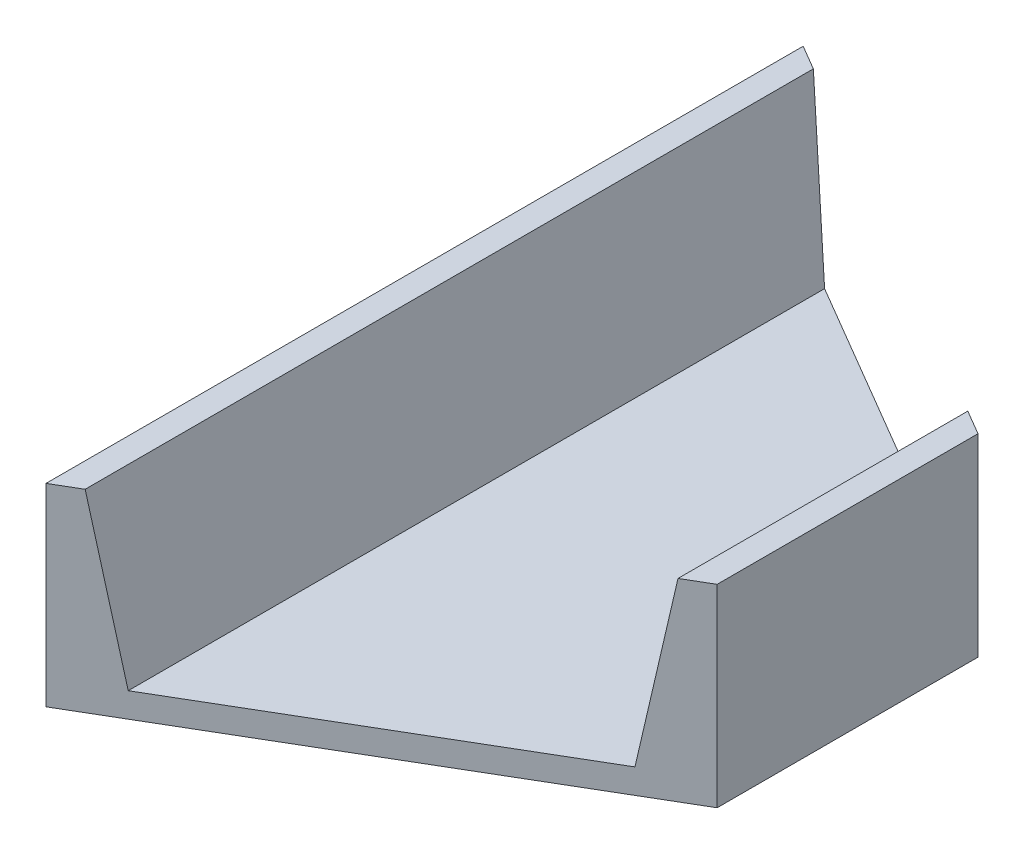
SolidWorks part; units mm, degrees
ref_plane "Front Plane" through (0, 0, 0) normal (0, 0, 1) x (1, 0, 0)
ref_plane "Top Plane" through (0, 0, 0) normal (0, 1, 0) x (1, 0, 0)
ref_plane "Right Plane" through (0, 0, 0) normal (1, 0, 0) x (0, 0, -1)
sketch "Sketch1" plane through (0, 0, 0) normal (0, 0, 1) x (1, 0, 0)
  line L0 (-28.7655, -12.9858) -> (28.7655, -12.9858)
  line L1 (38.1, 17.4308) -> (-38.1, 17.4307) construction
  line L2 (38.1, 17.4308) -> (38.1, -17.4307)
  line L3 (38.1, -17.4307) -> (-38.1, -17.4308)
  line L4 (-38.1, 17.4307) -> (-38.1, -17.4308)
  line L5 (38.1, 17.4308) -> (-38.1, -17.4308) construction
  line L6 (38.1, -17.4307) -> (-38.1, 17.4307) construction
  line L7 (28.7655, -12.9858) -> (33.655, 17.4308)
  line L8 (-33.655, 17.4307) -> (-28.7655, -12.9858)
  line L9 (-38.1, 17.4307) -> (-33.655, 17.4307)
  line L10 (33.655, 17.4308) -> (38.1, 17.4308)
  point P0 (0, 0)
  dimension "D1" = 34.8615
  dimension "D2" = 76.2
  dimension "D3" = 4.445
  dimension "D4" = 9.3345
  dimension "D5" = 9.3345
  dimension "D6" = 4.445
  dimension "D7" = 4.445
extrude "Boss-Extrude1" add sketch "Sketch1" along normal blind 136.398
sketch "Sketch2" plane through (0, 0, 0) normal (0, 1, 0) x (1, 0, 0)
  line L0 (-38.1, 0) -> (38.1, -44.704)
  line L2 (38.1, -136.398) -> (38.1, 0) construction
  line L3 (-38.1, -136.398) -> (38.1, -91.694)
  line L4 (38.1, -44.704) -> (38.1, 0)
  line L5 (38.1, 0) -> (-38.1, 0)
  line L6 (38.1, -91.694) -> (38.1, -136.398)
  line L7 (38.1, -136.398) -> (-38.1, -136.398)
  dimension "D1" = 46.99
extrude "Cut-Extrude1" cut sketch "Sketch2" against normal through all and the other way through all
